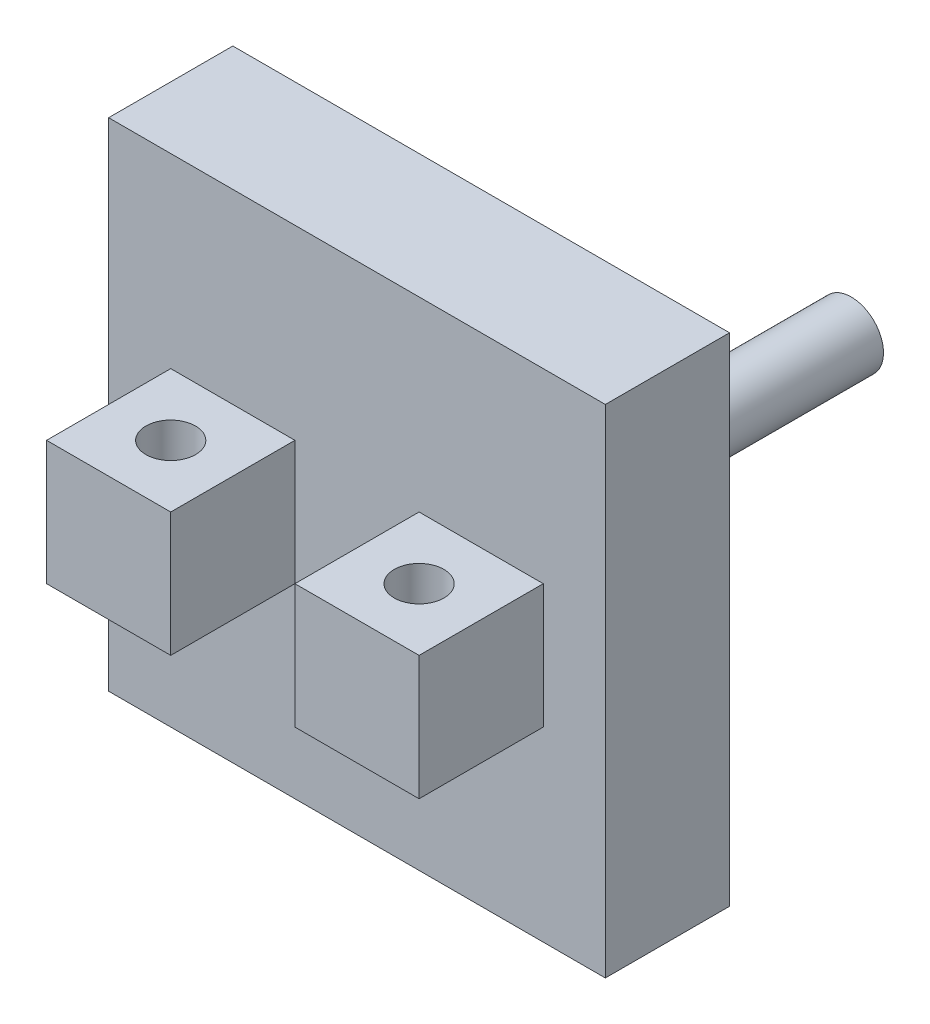
SolidWorks part; units mm, degrees
material "Cast Stainless Steel"
ref_plane "Front Plane" through (0, 0, 0) normal (0, 0, 1) x (1, 0, 0)
ref_plane "Top Plane" through (0, 0, 0) normal (0, 1, 0) x (1, 0, 0)
ref_plane "Right Plane" through (0, 0, 0) normal (1, 0, 0) x (0, 0, -1)
sketch "Sketch2" plane through (0, 0, 0) normal (0, 1, 0) x (1, 0, 0)
  line L0 (0, 0) -> (50, 0)
  line L1 (0, 0) -> (150, 0)
  line L2 (0, 0) -> (0, 100)
  line L3 (0, 100) -> (150, 100)
  line L4 (150, 0) -> (150, 100)
  line L5 (50, 0) -> (100, 0)
  line L6 (50, 0) -> (50, 50)
  line L7 (50, 50) -> (100, 50)
  line L8 (100, 50) -> (100, 0)
  dimension "D1" = 150
  dimension "D2" = 100
  dimension "D3" = 50
  dimension "D4" = 50
extrude "Boss-Extrude1" add sketch "Sketch2" along normal blind 50 contours L7 L8 L1 L4 L3 L2 L0 L6
sketch "Sketch3" plane through (0, 50, 0) normal (0, 1, 0) x (1, 0, 0)
  circle A0 centre (125, 25) radius 10
  circle A1 centre (25, 25) radius 10
  dimension "D1" = 20
  dimension "D2" = 20
extrude "Cut-Extrude1" cut sketch "Sketch3" against normal blind 50
sketch "Sketch4" plane through (0, 50, 0) normal (0, 1, 0) x (1, 0, 0)
  line L0 (150, 0) -> (150, 100) construction
  line L1 (150, 50) -> (0, 50)
  line L2 (150, 50) -> (150, 100)
  line L3 (150, 100) -> (0, 100)
  line L4 (0, 50) -> (0, 100)
extrude "Boss-Extrude2" add sketch "Sketch4" along normal blind 50
sketch "Sketch5" plane through (0, 0, 0) normal (0, -1, 0) x (1, 0, 0)
  line L0 (150, 0) -> (150, -100) construction
  line L1 (150, -50) -> (0, -50)
  line L2 (150, -50) -> (150, -100)
  line L3 (150, -100) -> (0, -100)
  line L4 (0, -50) -> (0, -100)
extrude "Boss-Extrude3" add sketch "Sketch5" along normal blind 50
sketch "Sketch6" plane through (0, 0, -100) normal (0, 0, -1) x (-1, 0, 0)
  line L0 (0, 100) -> (0, -50) construction
  line L1 (-150, 100) -> (0, 100)
  line L2 (-150, 100) -> (-150, -50)
  line L3 (-150, -50) -> (0, -50)
  line L4 (0, 100) -> (0, -50)
  line L8 (-150, 125) -> (-175, 125)
  line L9 (-175, 100) -> (-175, 125)
  line L10 (0, -50) -> (25, -50)
  line L11 (0, -50) -> (0, -75)
  line L12 (0, -75) -> (25, -75)
  line L13 (25, -50) -> (25, -75)
  line L14 (-175, 125) -> (25, 125)
  line L15 (-175, 125) -> (-175, -75)
  line L16 (-175, -75) -> (25, -75)
  line L17 (25, 125) -> (25, -75)
  dimension "D1" = 25
  dimension "D2" = 25
  dimension "D3" = 25
  dimension "D4" = 25
extrude "Boss-Extrude4" add sketch "Sketch6" against normal blind 50
sketch "Sketch7" plane through (0, 0, -100) normal (0, 0, -1) x (-1, 0, 0)
  line L0 (-175, -75) -> (-175, 125) construction
  circle A0 centre (-100, 25) radius 32
  point P2 (0, 0)
  dimension "D1" = 64
  dimension "D2" = 75
extrude "Boss-Extrude5" add sketch "Sketch7" along normal blind 12
sketch "Sketch8" plane through (0, 0, -112) normal (0, 0, -1) x (-1, 0, 0)
  circle A0 centre (-100, 25) radius 13
  dimension "D1" = 26
extrude "Boss-Extrude6" add sketch "Sketch8" along normal blind 112
